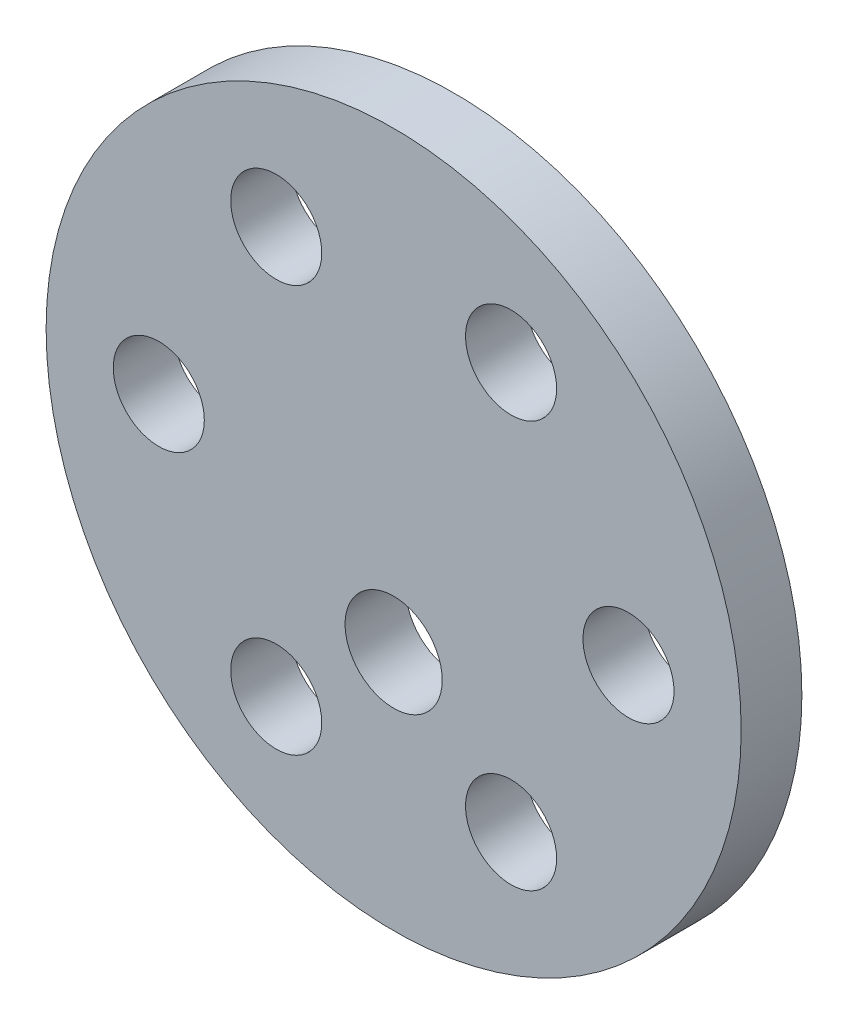
SolidWorks part; units mm, degrees
ref_plane "Front Plane" through (0, 0, 0) normal (0, 0, 1) x (1, 0, 0)
ref_plane "Top Plane" through (0, 0, 0) normal (0, 1, 0) x (1, 0, 0)
ref_plane "Right Plane" through (0, 0, 0) normal (1, 0, 0) x (0, 0, -1)
sketch "Sketch2" plane through (0, 0, 0) normal (0, 0, 1) x (1, 0, 0)
  line L0 (0, 0) -> (15.475, 0) construction
  circle A0 centre (0, 0) radius 22.9
  circle A1 centre (15.475, 0) radius 3
  circle A2 centre (7.7375, -13.4017) radius 3
  circle A3 centre (-7.7375, -13.4017) radius 3
  circle A4 centre (-15.475, 0) radius 3
  circle A5 centre (-7.7375, 13.4017) radius 3
  circle A6 centre (7.7375, 13.4017) radius 3
  circle A8 centre (0, -7) radius 3.2
  point P0 (-0.0192, -8.3929)
  point P6 (0, 0)
  dimension "D1" = 6
  dimension "D6" = 6.4
  dimension "D7" = 45.8
  dimension "D2" = 15.475
  dimension "D4" = 15.475
  dimension "D5" = 7
  dimension "D3" = 6
extrude "Boss-Extrude1" add sketch "Sketch2" along normal blind 4
